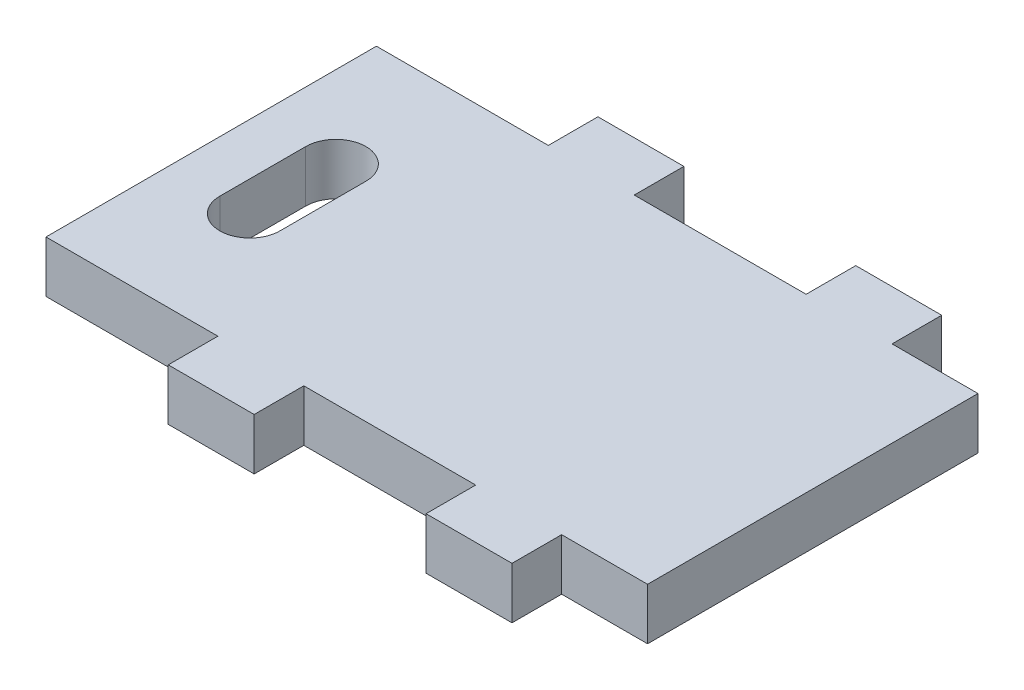
SolidWorks part; units mm, degrees
ref_plane "Front Plane" through (0, 0, 0) normal (0, 0, 1) x (1, 0, 0)
ref_plane "Top Plane" through (0, 0, 0) normal (0, 1, 0) x (1, 0, 0)
ref_plane "Right Plane" through (0, 0, 0) normal (1, 0, 0) x (0, 0, -1)
sketch "Sketch1" plane through (0, 0, 0) normal (0, 1, 0) x (1, 0, 0)
  line L0 (-25, 25) -> (-25, -25)
  line L1 (-35, 25) -> (35, 25)
  line L2 (-35, 25) -> (-35, -25)
  line L3 (-35, -25) -> (35, -25)
  line L4 (35, 25) -> (35, -25)
  line L5 (-35, 25) -> (35, -25) construction
  line L6 (-35, -25) -> (35, 25) construction
  point P0 (0, 0)
  dimension "D2" = 50
  dimension "D1" = 70
  dimension "D3" = 10
sketch "Sketch2" plane through (0, 0, 0) normal (0, 0, 1) x (1, 0, 0)
  line L0 (0, 0) -> (0, 6) construction
  line L1 (-35, 0) -> (35, 0) construction
  dimension "D1" = 6
extrude "Boss-Extrude1" add sketch "Sketch1" along normal up to vertex (6 mm away) contours L4 L1 L0 L3 up to point (0, 6, 0)
sketch "Sketch3" plane through (0, 6, 0) normal (0, 1, 0) x (1, 0, 0)
  line L0 (-25, 25) -> (35, 25) construction
  line L1 (35, 25) -> (25, 25)
  line L2 (35, 25) -> (35, 19.2244)
  line L3 (35, 19.2244) -> (25, 19.2244)
  line L4 (25, 25) -> (25, 19.2244)
  line L5 (25, 19.2244) -> (15, 19.2244) construction
  line L6 (25, 19.2244) -> (25, 25) construction
  line L7 (25, 25) -> (15, 25) construction
  line L8 (15, 19.2244) -> (15, 25) construction
  line L10 (15, 25) -> (-5, 25)
  line L11 (15, 25) -> (15, 19.2244)
  line L12 (15, 19.2244) -> (-5, 19.2244)
  line L13 (-5, 25) -> (-5, 19.2244)
  line L18 (-5, 19.2244) -> (-15, 19.2244) construction
  line L19 (-5, 19.2244) -> (-5, 25) construction
  line L20 (-5, 25) -> (-15, 25) construction
  line L21 (-15, 19.2244) -> (-15, 25) construction
  line L22 (-25, 25) -> (-15, 25)
  line L23 (-25, 25) -> (-25, 19.2244)
  line L24 (-25, 19.2244) -> (-15, 19.2244)
  line L25 (-15, 25) -> (-15, 19.2244)
  dimension "D1" = 10
  dimension "D2" = 20
  dimension "D3" = 5.7756
extrude "Cut-Extrude2" cut sketch "Sketch3" against normal through all
mirror "Mirror2" about plane through (0, 0, 0) normal (0, 0, 1) of "Cut-Extrude2"
sketch "Sketch4" plane through (0, 6, 0) normal (0, 1, 0) x (1, 0, 0)
  line L1 (-25, -19.2244) -> (-35, -19.2244)
  line L2 (-25, -19.2244) -> (-25, 19.2244)
  line L3 (-25, 19.2244) -> (-35, 19.2244)
  line L4 (-35, -19.2244) -> (-35, 19.2244)
  point P8 (-35, -19)
extrude "Boss-Extrude2" add sketch "Sketch4" against normal up to surface (6 mm away) contours L3 L4 L1 L2 up to face at (5, 0, 0)
sketch "Sketch5" plane through (0, 6, 0) normal (0, 1, 0) x (1, 0, 0)
  line L0 (-25.5, -5) -> (-25.5, 5) construction
  line L1 (-29, -5) -> (-29, 5)
  line L2 (-22, -5) -> (-22, 5)
  line L3 (-25.5, 0) -> (0, 0) construction
  line L4 (-29, 0) -> (-35, 0)
  line L5 (-35, -19.2244) -> (-35, 19.2244) construction
  arc A0 (-29, -5) -> (-22, -5) centre (-25.5, -5) ccw
  arc A1 (-22, 5) -> (-29, 5) centre (-25.5, 5) ccw
  point P2 (-25.5, 0)
  dimension "D1" = 6
  dimension "D2" = 7
  dimension "D3" = 10
extrude "Cut-Extrude3" cut sketch "Sketch5" against normal through all contours L2 A1 L1 A0
equation "\"glass_width\"= 150"
equation "\"glass_height\"= 100"
equation "\"glass_thickness\"= 4"
equation "\"brood_space\"= 42"
equation "\"t1\"= 6"
equation "\"t2\"= 3.2"
equation "\"box_depth\"= \"brood_space\" + \"glass_thickness\" + \"glass_thickness\" + \"t2\" + \"t2\""
equation "\"box_width\"= \"glass_width\" + \"t1\" + \"t1\""
equation "\"food_height\"= 70"
equation "\"box_height\"= \"glass_height\" + ( \"t1\" * 3 ) + \"food_height\""
equation "\"D1@Sketch2\"=\"t1\""
equation "\"D2@Sketch1\"=\"glass_thickness\"+\"glass_thickness\"+\"brood_space\""
equation "\"D1@Sketch1\"=\"food_height\""
